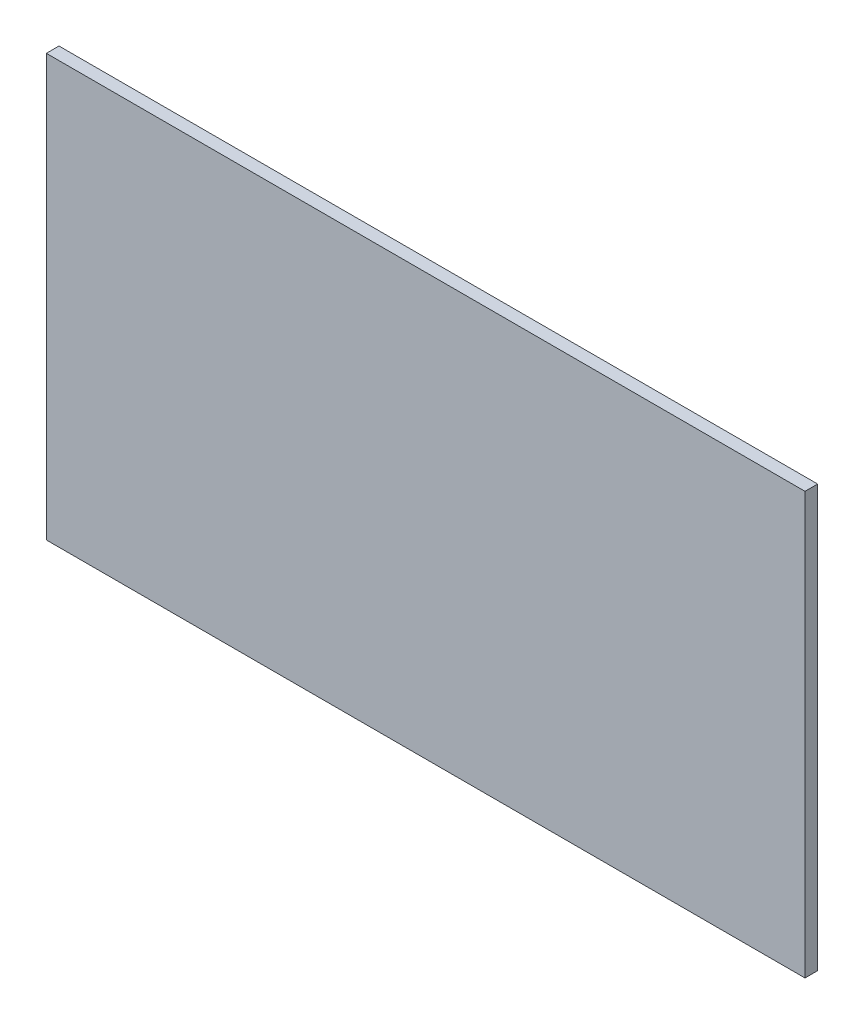
SolidWorks part; units mm, degrees
ref_plane "Alzado" through (0, 0, 0) normal (0, 0, 1) x (1, 0, 0)
ref_plane "Planta" through (0, 0, 0) normal (0, 1, 0) x (1, 0, 0)
ref_plane "Vista lateral" through (0, 0, 0) normal (1, 0, 0) x (0, 0, -1)
sketch "Croquis1" plane through (0, 0, 0) normal (0, 0, 1) x (1, 0, 0)
  line L1 (0, 0) -> (180, 0)
  line L2 (0, 0) -> (0, 100)
  line L3 (0, 100) -> (180, 100)
  line L4 (180, 0) -> (180, 100)
  dimension "D1" = 100
  dimension "D2" = 180
extrude "Saliente-Extruir1" add sketch "Croquis1" along normal blind 3
